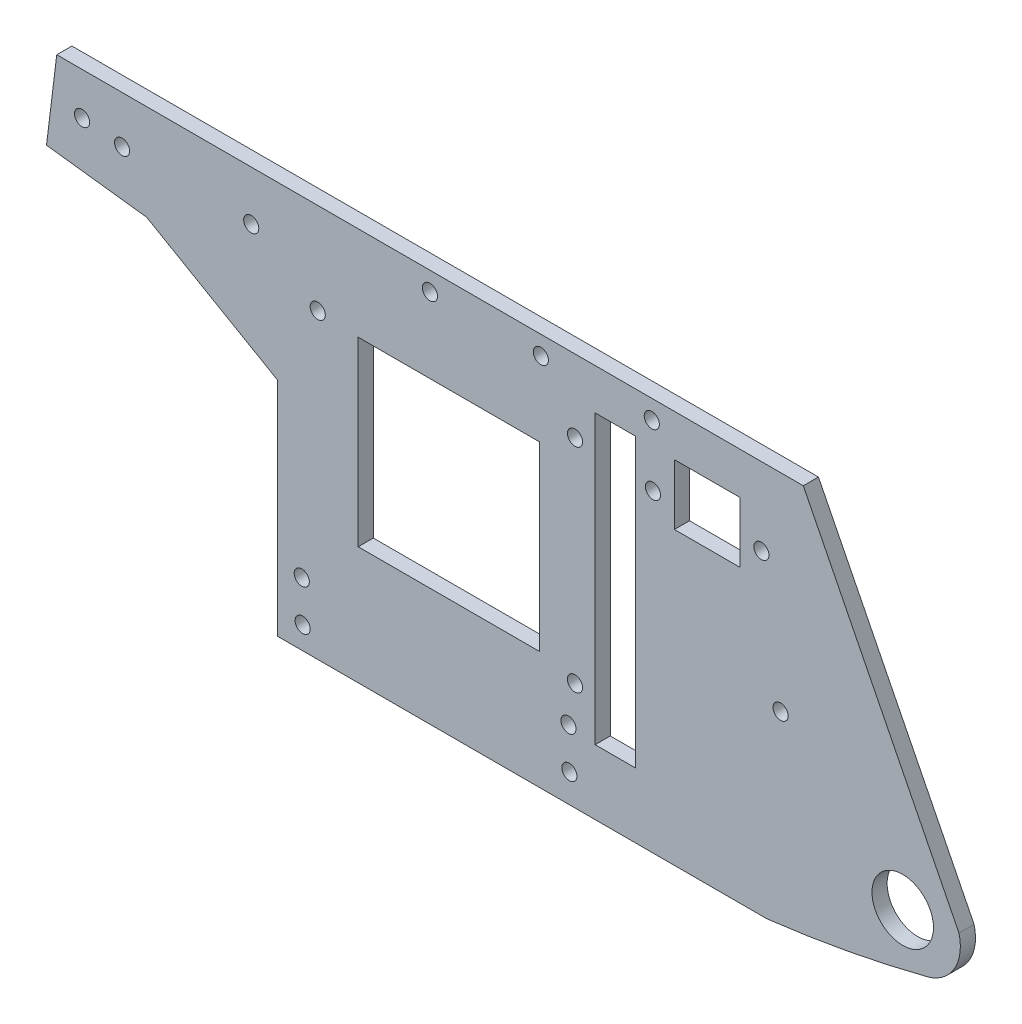
SolidWorks part; units mm, degrees
ref_plane "前视基准面" through (0, 0, 0) normal (0, 0, 1) x (1, 0, 0)
ref_plane "上视基准面" through (0, 0, 0) normal (0, 1, 0) x (1, 0, 0)
ref_plane "右视基准面" through (0, 0, 0) normal (1, 0, 0) x (0, 0, -1)
sketch "草图1" plane through (0, 0, 0) normal (0, 0, 1) x (1, 0, 0)
  line L0 (30.3675, 31.7981) -> (153.7284, 31.7981)
  line L2 (146.5277, -46.2019) -> (49.4494, -46.2019)
  line L5 (153.7284, 31.7981) -> (184.6028, -29.5956)
  line L6 (92.048, 31.7981) -> (92.048, -46.2019) construction
  line L7 (92.048, -7.2019) -> (144.0701, -7.2019) construction
  line L8 (92.048, -7.2019) -> (95.382, -7.2019) construction
  line L9 (95.382, -7.2019) -> (95.382, 6.7981) construction
  line L10 (95.382, 6.7981) -> (60.382, 6.7981) construction
  line L11 (60.382, 6.7981) -> (60.382, -21.2019) construction
  line L12 (60.382, -21.2019) -> (95.382, -21.2019) construction
  line L13 (95.382, -21.2019) -> (95.382, -7.2019) construction
  line L14 (23.4686, 12.7981) -> (49.4494, -2.2019)
  line L15 (49.4494, -2.2019) -> (49.4494, -46.2019)
  line L16 (30.3675, 31.7981) -> (5.6596, 31.7981)
  line L20 (23.4686, 12.7981) -> (3.6177, 15.2355)
  line L23 (3.6177, 15.2355) -> (5.6513, 31.7981)
  line L24 (5.6513, 31.7981) -> (5.6596, 31.7981)
  arc A4 (184.6028, -29.5956) -> (178.3201, -40.2482) centre (176.1446, -31.7862) cw
  arc A5 (178.3201, -40.2482) -> (146.5277, -46.2019) centre (117.7324, 195.4245) cw
  point P7 (181.997, -46.4446)
  point P14 (-18.003, -46.4446)
  point P17 (26.8048, 31.7981)
  dimension "D4" = 120
  dimension "D5" = 123.3609
  dimension "D3" = 116.697
  dimension "D6" = 44
  dimension "D15" = 8.7372
  dimension "D16" = 243.3362
  dimension "D2" = 157
  dimension "160" = 200
  dimension "D7" = 78
  dimension "D8" = 35
  dimension "D9" = 14
  dimension "D10" = 14
  dimension "D11" = 20
  dimension "D12" = 97.0783
  dimension "D13" = 68.7198
  dimension "D14" = 30
extrude "凸台-拉伸1" add sketch "草图1" along normal blind 3
sketch "草图2" plane through (0, 0, 3) normal (0, 0, 1) x (1, 0, 0)
  line L0 (92.4143, -41.5608) -> (92.4143, 33.4392) construction
  line L5 (49.4494, -2.2019) -> (49.4494, -46.2019) construction
  line L7 (92.4143, -4.0608) -> (46.7593, -4.0608) construction
  line L26 (65.4399, 13.1727) -> (101.4399, 13.1727)
  line L32 (65.4399, 13.1727) -> (65.4399, -22.8273)
  line L33 (65.4399, -22.8273) -> (101.4399, -22.8273)
  line L34 (101.4399, 13.1727) -> (101.4399, -22.8273)
  line L35 (101.4399, -4.8273) -> (112.4399, -4.8273) construction
  line L36 (112.4399, -4.8273) -> (112.4399, -33.3273)
  line L37 (112.4399, -33.3273) -> (120.4399, -33.3273)
  line L38 (120.4399, -33.3273) -> (120.4399, 23.6727)
  line L39 (120.4399, 23.6727) -> (112.4399, 23.6727)
  line L40 (112.4399, 23.6727) -> (112.4399, -4.8273)
  circle A3 centre (173.4494, -31.2019) radius 6.1
  dimension "D6" = 12.2
  dimension "D8" = 124
  dimension "D1" = 36
  dimension "D2" = 36
  dimension "D3" = 11
  dimension "D4" = 57
  dimension "D5" = 8
  dimension "D7" = 63
extrude "切除-拉伸1" cut sketch "草图2" against normal up to next
sketch "草图3" plane through (0, 0, 3) normal (0, 0, 1) x (1, 0, 0)
  line L2 (101.4399, 19.9563) -> (101.4399, -25.0437)
  line L3 (101.4399, -25.0437) -> (105.4399, -25.0437)
  line L4 (105.4399, 19.9563) -> (105.4399, -25.0437)
  line L5 (101.4399, 19.9563) -> (101.4399, 23.6727)
  line L6 (101.4399, 23.6727) -> (112.4399, 23.6727)
  line L7 (112.4399, 23.6727) -> (112.4399, 19.9563)
  line L8 (112.4399, 23.6727) -> (112.4399, -33.3273) construction
  line L9 (112.4399, 19.9563) -> (105.4399, 19.9563)
  dimension "D1" = 4
  dimension "D2" = 45
hole_wizard "大小mm Clearance 暗销孔1" positions "草图4" profile "草图5" hole size "Ø3.0" standard "ISO" end condition through all
sketch "草图4" plane through (141.6737, 151.8582, 3) normal (0, 0, 1) x (-0.9998, -0.021, 0)
  point P0 (20.5912, 123.3982)
  point P2 (42.5912, 122.9368)
  point P4 (64.5816, 122.4756)
sketch "草图5" plane through (123.6745, 28.0554, 3) normal (1, 0, 0) x (0, -1, 0)
  line L0 (0, 0) -> (0, 3)
  line L1 (0, 3) -> (1.5, 3)
  line L2 (1.5, 3) -> (1.5, 0)
  line L3 (1.5, 0) -> (0, 0)
  line L4 (0, -6.35) -> (0, 107.95) construction
  dimension "通孔孔直径" = 3
  dimension "通孔孔深度" = 3
hole_wizard "大小mm Clearance 暗销孔4" positions "草图10" profile "草图11" hole size "Ø3.0" standard "ISO" end condition through all
sketch "草图10" plane through (141.6737, 151.8582, 3) normal (0, 0, 1) x (-0.9998, -0.021, 0)
  point P0 (20.6088, 135.4526)
  point P2 (-0.9003, 135.4526)
sketch "草图11" plane through (123.9096, 16.0033, 3) normal (1, 0, 0) x (0, -1, 0)
  line L0 (0, 0) -> (0, 3)
  line L1 (0, 3) -> (1.5, 3)
  line L2 (1.5, 3) -> (1.5, 0)
  line L3 (1.5, 0) -> (0, 0)
  line L4 (0, -6.35) -> (0, 107.95) construction
  dimension "通孔孔直径" = 3
  dimension "通孔孔深度" = 3
sketch "草图18" plane through (0, 0, 3) normal (0, 0, 1) x (1, 0, 0)
  circle A0 centre (149.2228, -9.259) radius 1.5
  dimension "D1" = 3
extrude "切除-拉伸2" cut sketch "草图18" against normal up to next
hole_wizard "大小mm Clearance 暗销孔6" positions "草图19" profile "草图20" hole size "Ø3.0" standard "ISO" end condition through all
sketch "草图19" plane through (141.6737, 151.8582, 3) normal (0, 0, 1) x (-0.9998, -0.021, 0)
  point P0 (36.0454, 133.7091)
  point P3 (36.0454, 133.7091)
  point P5 (36.9307, 175.9191)
sketch "草图20" plane through (108.4399, 17.4227, 3) normal (1, 0, 0) x (0, -1, 0)
  line L0 (0, 0) -> (0, 3)
  line L1 (0, 3) -> (1.5, 3)
  line L2 (1.5, 3) -> (1.5, 0)
  line L3 (1.5, 0) -> (0, 0)
  line L4 (0, -6.35) -> (0, 107.95) construction
  dimension "通孔孔直径" = 3
  dimension "通孔孔深度" = 3
sketch "草图21" plane through (0, 0, 3) normal (0, 0, 1) x (1, 0, 0)
  line L0 (123.9096, 16.0033) -> (128.1618, 16.0033) construction
  line L1 (128.1618, 23.5033) -> (141.1618, 23.5033)
  line L2 (128.1618, 23.5033) -> (128.1618, 11.5033)
  line L3 (128.1618, 11.5033) -> (141.1618, 11.5033)
  line L4 (141.1618, 23.5033) -> (141.1618, 11.5033)
  line L5 (145.414, 16.4543) -> (141.1618, 16.4543) construction
  line L6 (134.6618, 16.0033) -> (128.1618, 16.0033) construction
  dimension "D1" = 13
  dimension "D2" = 12
extrude "切除-拉伸3" cut sketch "草图21" against normal up to next
hole_wizard "大小mm Clearance 暗销孔7" positions "草图24" profile "草图25" hole size "Ø3.0" standard "ISO" end condition through all
sketch "草图24" plane through (143.3212, 150.868, 3) normal (0, 0, 1) x (-0.9998, -0.0223, 0)
  point P0 (88.939, 135.2274)
  point P3 (101.9425, 126.6475)
  point P6 (127.5376, 125.5988)
  point P9 (135.4543, 124.4474)
sketch "草图25" plane through (57.4135, 13.695, 3) normal (1, 0, 0) x (0, -1, 0)
  line L0 (0, 0) -> (0, 3)
  line L1 (0, 3) -> (1.5, 3)
  line L2 (1.5, 3) -> (1.5, 0)
  line L3 (1.5, 0) -> (0, 0)
  line L4 (0, -6.35) -> (0, 107.95) construction
  dimension "通孔孔直径" = 3
  dimension "通孔孔深度" = 3
hole_wizard "大小mm Clearance 暗销孔10" positions "草图30" profile "草图31" hole size "Ø3.0" standard "ISO" end condition through all
sketch "草图30" plane through (143.3212, 150.868, 3) normal (0, 0, 1) x (-0.9998, -0.0223, 0)
  point P0 (93.1614, 190.5782)
  point P2 (93.1614, 182.5471)
  point P4 (40.2454, 190.5782)
  point P5 (40.2454, 182.5471)
sketch "草图31" plane through (54.4239, -41.7361, 3) normal (1, 0, 0) x (0, -1, 0)
  line L0 (0, 0) -> (0, 3)
  line L1 (0, 3) -> (1.5, 3)
  line L2 (1.5, 3) -> (1.5, 0)
  line L3 (1.5, 0) -> (0, 0)
  line L4 (0, -6.35) -> (0, 107.95) construction
  dimension "通孔孔直径" = 3
  dimension "通孔孔深度" = 3
